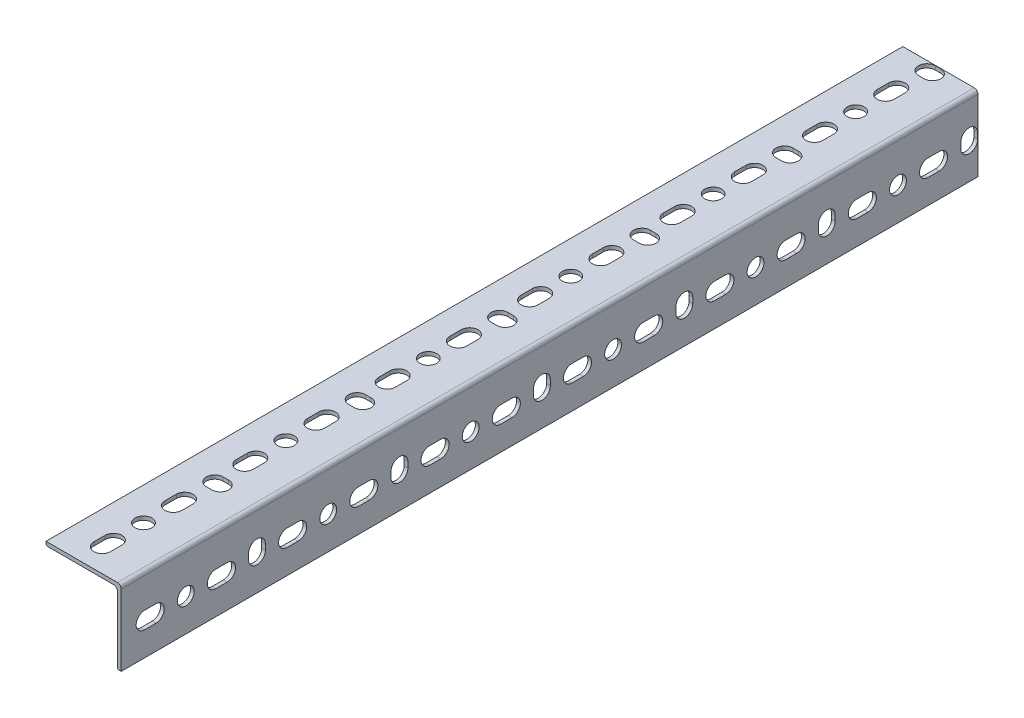
SolidWorks part; units mm, degrees
material "Black Iron Steel"
ref_plane "Front Plane" through (0, 0, 0) normal (0, 0, 1) x (1, 0, 0)
ref_plane "Top Plane" through (0, 0, 0) normal (0, 1, 0) x (1, 0, 0)
ref_plane "Right Plane" through (0, 0, 0) normal (1, 0, 0) x (0, 0, -1)
other "Length"
sketch "Length Changing Spot" plane through (0, 0, 0) normal (0, 1, 0) x (1, 0, 0)
  line L0 (0, 0) -> (0, 457.2)
  dimension "D1" = 457.2
other "Structural Member1"
ref_plane "Plane1" through (0, 0, 0) normal (0, 0, -1) x (-1, 0, 0)
sketch "Sketch13" plane through (0, 0, 0) normal (0, 0, -1) x (-1, 0, 0)
  line L0 (40.1, 0) -> (2, 0)
  line L1 (0, -2) -> (0, -40.1)
  line L2 (39.1, -2) -> (4, -2)
  line L3 (2, -4) -> (2, -39.1)
  line L4 (40.1, 0) -> (40.1, -1)
  line L5 (0, -40.1) -> (1, -40.1)
  arc A0 (40.1, -1) -> (39.1, -2) centre (39.1, -1) cw
  arc A1 (1, -40.1) -> (2, -39.1) centre (1, -39.1) ccw
  arc A2 (4, -2) -> (2, -4) centre (4, -4) ccw
  arc A3 (2, 0) -> (0, -2) centre (2, -2) ccw
  point P2 (21.05, 0)
  point P13 (0, -21.05)
  point P17 (0, 0)
  point P18 (0, 0)
  dimension "r1" = 1
  dimension "r" = 2
  dimension "D1" = 2
  dimension "b" = 40.1
  dimension "d" = 2
sketch "Sketch3" plane through (0, 0, 0) normal (0, 1, 0) x (1, 0, 0)
  line L0 (-22.6, 12.5) -> (-22.6, 18.5) construction
  line L1 (-27.1, 12.5) -> (-27.1, 18.5)
  line L2 (-18.1, 12.5) -> (-18.1, 18.5)
  line L3 (-40.1, 0) -> (-2, 0) construction
  line L4 (-40.1, 457.2) -> (-40.1, 0) construction
  arc A0 (-27.1, 12.5) -> (-18.1, 12.5) centre (-22.6, 12.5) ccw
  arc A1 (-18.1, 18.5) -> (-27.1, 18.5) centre (-22.6, 18.5) ccw
  point P2 (-22.6, 15.5)
  dimension "D1" = 15
  dimension "D3" = 8
  dimension "D2" = 9
  dimension "D4" = 13
extrude "Slot" cut sketch "Sketch3" against normal through all
sketch "Sketch4" plane through (0, 0, 0) normal (0, 1, 0) x (1, 0, 0)
  line L0 (-22.6, 34.5) -> (-22.6, 15.5) construction
  line L1 (-22.6, 12.5) -> (-22.6, 18.5) construction
  circle A0 centre (-22.6, 34.5) radius 4.5
  arc A1 (-18.1, 18.5) -> (-27.1, 18.5) centre (-22.6, 18.5) ccw construction
  dimension "D1" = 7
  dimension "D2" = 9
extrude "Hole" cut sketch "Sketch4" against normal through all
sketch "Sketch14" plane through (0, 0, 0) normal (0, 1, 0) x (1, 0, 0)
  line L0 (-19.6, 72.5) -> (-22.6, 72.5) construction
  line L1 (-19.6, 68) -> (-22.6, 68)
  line L2 (-19.6, 77) -> (-22.6, 77)
  arc A0 (-19.6, 68) -> (-19.6, 77) centre (-19.6, 72.5) ccw
  arc A1 (-22.6, 77) -> (-22.6, 68) centre (-22.6, 72.5) ccw
  point P2 (-21.1, 72.5)
  dimension "D2" = 12
  dimension "D1" = 9
  dimension "D3" = 38
extrude "Vert Slot" cut sketch "Sketch14" against normal through all
pattern_linear "Slot Pattern" count 12 spacing 38 along (0, 0, -1) of "Slot"
pattern_linear "Hole Pattern" count 6 spacing 76 along (0, 0, -1) of "Hole"
pattern_linear "LPattern1" count 6 spacing 76 along (0, 0, -1) of "Vert Slot"
pattern_circular "Other side cuts" count 2 every 90 about axis through (-4, -4, 0) along (0, 0, 1) of "Slot", "Hole", "Vert Slot", "Slot Pattern", "Hole Pattern", "LPattern1"
equation "\"D1@Sketch13\" = \"r@Sketch13\""
